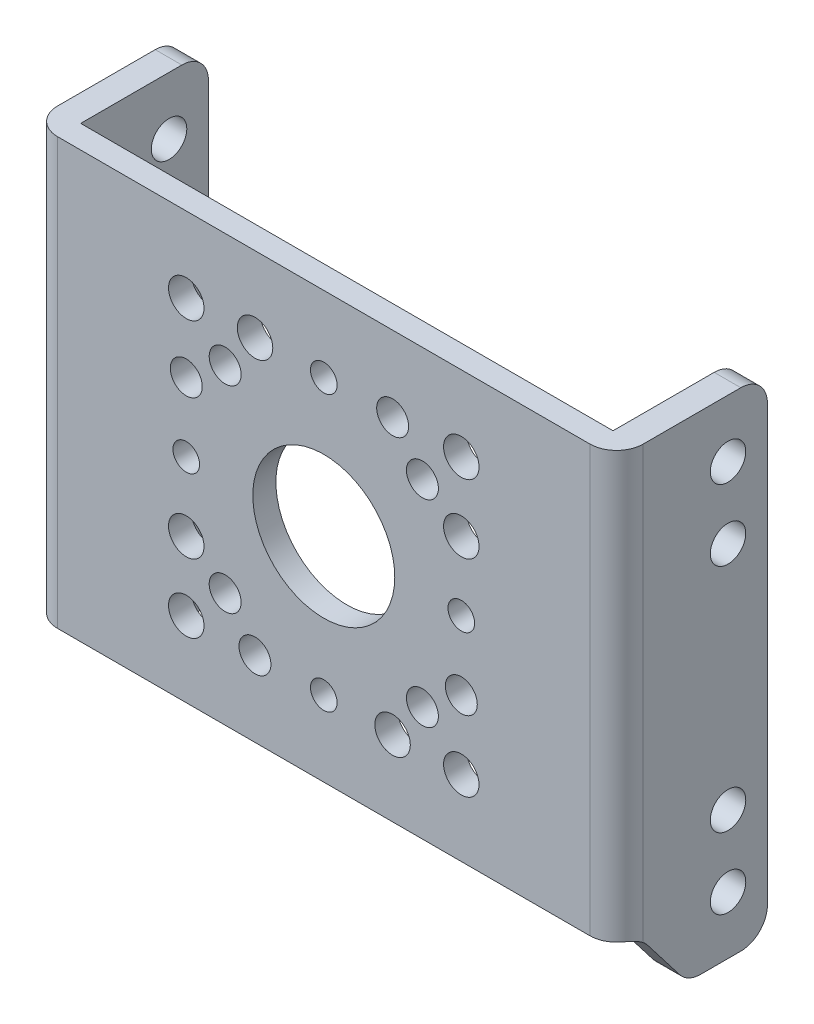
SolidWorks part; units mm, degrees
material "1060 Alloy"
ref_plane "Front Plane" through (0, 0, 0) normal (0, 0, 1) x (1, 0, 0)
ref_plane "Top Plane" through (0, 0, 0) normal (0, 1, 0) x (1, 0, 0)
ref_plane "Right Plane" through (0, 0, 0) normal (1, 0, 0) x (0, 0, -1)
sketch "Sketch1" plane through (0, 0, 0) normal (0, 0, 1) x (1, 0, 0)
  line L0 (-7.75, 7.75) -> (7.75, 7.75) construction
  line L1 (-16.5, 12) -> (16.5, 12)
  line L2 (-16.5, 12) -> (-16.5, -12)
  line L3 (-16.5, -12) -> (16.5, -12)
  line L4 (16.5, 12) -> (16.5, -12)
  line L5 (-16.5, 12) -> (16.5, -12) construction
  line L6 (-16.5, -12) -> (16.5, 12) construction
  line L7 (-8.75, 8.75) -> (8.75, 8.75) construction
  line L8 (-8.75, 8.75) -> (-8.75, -8.75) construction
  line L9 (-8.75, -8.75) -> (8.75, -8.75) construction
  line L10 (8.75, 8.75) -> (8.75, -8.75) construction
  line L11 (-8.75, 8.75) -> (8.75, -8.75) construction
  line L12 (-8.75, -8.75) -> (8.75, 8.75) construction
  circle A0 centre (0, 0) radius 4
  circle A1 centre (-7.75, 7.75) radius 1
  circle A2 centre (7.75, 7.75) radius 1
  circle A3 centre (7.75, -7.75) radius 1
  circle A4 centre (-7.75, -7.75) radius 1
  circle A5 centre (0, 7.75) radius 0.75
  circle A6 centre (-3.875, 7.75) radius 1
  circle A7 centre (3.88, 7.75) radius 0.9
  circle A8 centre (-5.558, 5.558) radius 0.9
  circle A9 centre (7.75, 3.875) radius 1
  circle A10 centre (7.75, 0) radius 0.75
  circle A11 centre (7.75, -3.88) radius 0.9
  circle A12 centre (5.558, 5.558) radius 0.9
  circle A13 centre (3.875, -7.75) radius 1
  circle A14 centre (0, -7.75) radius 0.75
  circle A15 centre (-3.88, -7.75) radius 0.9
  circle A16 centre (5.558, -5.558) radius 0.9
  circle A17 centre (-7.75, -3.875) radius 1
  circle A18 centre (-7.75, 0) radius 0.75
  circle A19 centre (-7.75, 3.88) radius 0.9
  circle A20 centre (-5.558, -5.558) radius 0.9
  point P0 (0, 0)
  point P23 (0, 0)
  point P56 (0, 0)
  dimension "D3" = 17.5
  dimension "D4" = 4
  dimension "D5" = 2
  dimension "D6" = 3.875
  dimension "D7" = 3.88
  dimension "D8" = 3.1
  dimension "D1" = 33
  dimension "D2" = 24
  dimension "D9" = 4
extrude "Boss-Extrude1" add sketch "Sketch1" along normal blind 1.3
sketch "Sketch2" plane through (16.5, 0, 0) normal (1, 0, 0) x (0, 0, -1)
  line L0 (-1.3, 12) -> (5.7, 12)
  line L1 (7.2, 10.5) -> (7.2, -14)
  line L2 (5.7, -15.5) -> (3.4373, -15.5)
  line L3 (2.2496, -14.9162) -> (0.4504, -12.5838)
  line L4 (-0.7373, -12) -> (-1.3, -12)
  line L5 (-1.3, -12) -> (-1.3, 12)
  line L6 (-1.3, 12) -> (-1.3797, 11.9205)
  line L7 (4.98, 12) -> (4.98, -15.5) construction
  line L8 (-1.3, -1.75) -> (7.2, -1.75) construction
  arc A0 (0.4504, -12.5838) -> (-0.7373, -12) centre (-0.7373, -13.5) ccw
  arc A1 (5.7, 12) -> (7.2, 10.5) centre (5.7, 10.5) cw
  arc A2 (7.2, -14) -> (5.7, -15.5) centre (5.7, -14) cw
  arc A3 (3.4373, -15.5) -> (2.2496, -14.9162) centre (3.4373, -14) cw
  circle A4 centre (4.98, 8.75) radius 1
  circle A5 centre (4.98, 4.75) radius 1
  circle A6 centre (4.98, -8.25) radius 1
  circle A7 centre (4.98, -12.25) radius 1
  point P12 (0, -12)
  point P15 (7.2, 12)
  point P18 (7.2, -15.5)
  point P21 (2.7, -15.5)
  point P26 (4.98, -1.75)
  line M1 (0, -12) -> (0, 12)
  line M4 (-1.3, -12) -> (0, -12)
  dimension "D4" = 1.5
  dimension "D6" = 10.5
  dimension "D7" = 4
  dimension "D1" = 8.5
  dimension "D2" = 27.5
  dimension "D3" = 4.5
  dimension "D5" = 2.22
extrude "Boss-Extrude2" add sketch "Sketch2" against normal blind 1.5 contours A3 L2 A2 L1 A1 L0 A0 L3 A6 A5 A4 A7 M1 M4
mirror "Mirror1" about plane through (0, 0, 0) normal (1, 0, 0) of "Boss-Extrude2"
fillet "Fillet1" radius 1.5 2 edges at (-16.5, 0, 1.3) (16.5, 0, 1.3)
